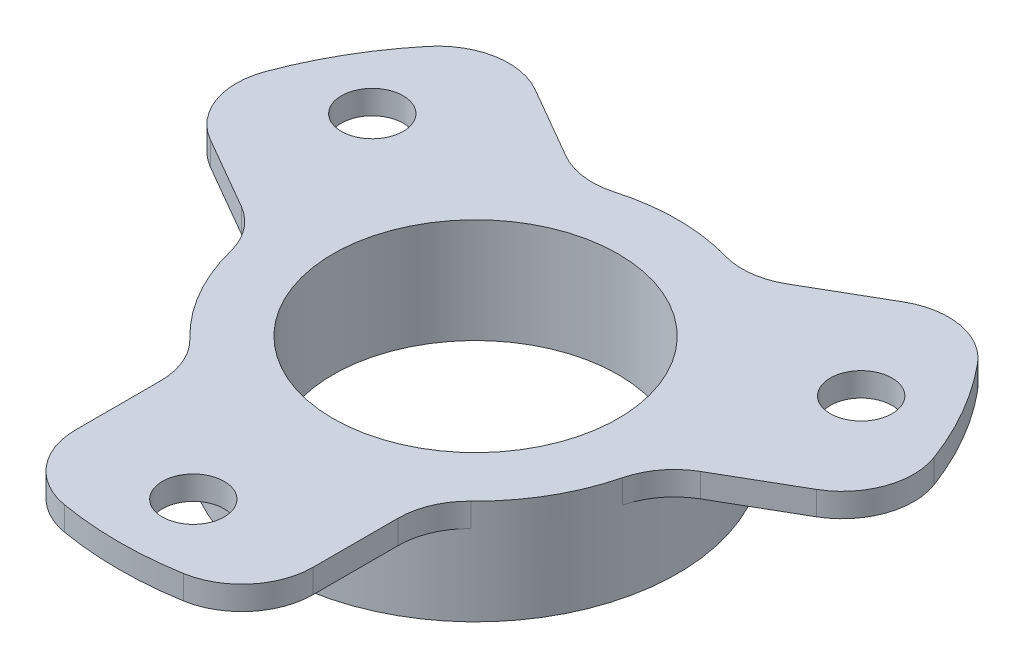
SolidWorks part; units mm, degrees
material "ABS"
ref_plane "Front Plane" through (0, 0, 0) normal (0, 0, 1) x (1, 0, 0)
ref_plane "Top Plane" through (0, 0, 0) normal (0, 1, 0) x (1, 0, 0)
ref_plane "Right Plane" through (0, 0, 0) normal (1, 0, 0) x (0, 0, -1)
sketch "Master Dimension Reference" plane through (0, 0, 0) normal (0, 1, 0) x (1, 0, 0)
  line L0 (0, 27.1168) -> (0, -27.1168) construction
  line L1 (-38.0934, 0) -> (38.0934, 0) construction
  line L2 (0, 0) -> (25.9808, 15) construction
  line L3 (0, 0) -> (-25.9808, 15) construction
  circle A0 centre (0, 0) radius 23.75 construction
  circle A1 centre (0, 0) radius 12 construction
  point P4 (0, 0)
  point P8 (0, 0)
  dimension "D1" = 47.5
  dimension "D2" = 24
sketch "Sketch2" plane through (0, 0, 0) normal (0, 0, 1) x (1, 0, 0)
  line L0 (-40, 0) -> (-17, 0)
  line L1 (-13.5, -6.8) -> (23.543, -6.8) construction
  line L2 (-15.5, -6.8) -> (-17, -6.8)
  line L3 (-38.0934, 0) -> (38.0934, 0) construction
  line L4 (0, 30.0771) -> (0, -30.0771) construction
  line L5 (-12, -18.8498) -> (-12, 22.8498) construction
  line L7 (-23.543, -6.8) -> (-15.5, -6.8) construction
  line L8 (12, 0) -> (-12, 0) construction
  line L9 (-23.75, -19.5868) -> (-23.75, 19.5868) construction
  line L10 (-40, -43.6771) -> (-40, 30.0771) construction
  line L11 (-12, 2) -> (-12, -6.8)
  line L12 (-12, -6.8) -> (-13.5, -6.8)
  line L13 (-17, -6.8) -> (-17, 0)
  line L14 (-17, -25.8462) -> (-17, 25.8462) construction
  line L15 (-40, 2) -> (-12, 2)
  line L16 (-40, 2) -> (-40, 0)
  line L17 (-15.5, 0) -> (-13.5, 0)
  line L19 (-13.5, -6.8) -> (-13.5, 0)
  line L20 (-15.5, -6.8) -> (-15.5, 0)
  point P11 (0, 0)
  point P16 (-12, 2)
  point P17 (0, -6.8)
  point P22 (-23.75, 0)
  point P25 (-40, -6.8)
  point P28 (-17, 0)
  dimension "D1" = 12
  dimension "D2" = 6.8
  dimension "D3" = 23.75
  dimension "D4" = 40
  dimension "D5" = 17
  dimension "D6" = 2
revolve "Revolve1" add sketch "Sketch2" angle 360 about L4
sketch "Top View Pattern Sketch" plane through (0, 0, 0) normal (0, 1, 0) x (1, 0, 0)
  line L0 (-10, -23.6643) -> (-10, -16.5227)
  line L1 (0, 27.1168) -> (0, -27.1168) construction
  line L2 (-19.3091, -0.3989) -> (-25.4939, 3.1719)
  line L3 (0, 0) -> (-25.9808, 15) construction
  line L4 (-9.3091, 16.9216) -> (-15.4939, 20.4924)
  line L5 (0, 17) -> (0, 39.2184) construction
  line L7 (9.3091, 16.9216) -> (15.4939, 20.4924)
  line L9 (19.3091, -0.3989) -> (25.4939, 3.1719)
  line L10 (10, -23.6643) -> (10, -16.5227)
  circle A18 centre (0, 0) radius 6
  arc A19 (-16.4893, -4.1355) -> (-11.8261, -12.2124) centre (0, 0) ccw
  arc A21 (-5, -29.5804) -> (5, -29.5804) centre (0, 0) ccw
  arc A22 (-23.1174, 19.1203) -> (-28.1174, 10.4601) centre (0, 0) ccw
  arc A23 (28.1174, 10.4601) -> (23.1174, 19.1203) centre (0, 0) ccw
  arc A24 (11.8261, -12.2124) -> (16.4893, -4.1355) centre (0, 0) ccw
  arc A25 (4.6632, 16.3479) -> (-4.6632, 16.3479) centre (0, 0) ccw
  arc A35 (-10, -23.6643) -> (-5, -29.5804) centre (-4, -23.6643) ccw
  arc A36 (-11.8261, -12.2124) -> (-10, -16.5227) centre (-16, -16.5227) cw
  arc A37 (-16.4893, -4.1355) -> (-19.3091, -0.3989) centre (-22.3091, -5.5951) ccw
  arc A38 (-25.4939, 3.1719) -> (-28.1174, 10.4601) centre (-22.4939, 8.3681) cw
  arc A39 (-23.1174, 19.1203) -> (-15.4939, 20.4924) centre (-18.4939, 15.2963) cw
  arc A40 (-9.3091, 16.9216) -> (-4.6632, 16.3479) centre (-6.3091, 22.1178) ccw
  arc A41 (4.6632, 16.3479) -> (9.3091, 16.9216) centre (6.3091, 22.1178) ccw
  arc A42 (15.4939, 20.4924) -> (23.1174, 19.1203) centre (18.4939, 15.2963) cw
  arc A43 (28.1174, 10.4601) -> (25.4939, 3.1719) centre (22.4939, 8.3681) cw
  arc A44 (19.3091, -0.3989) -> (16.4893, -4.1355) centre (22.3091, -5.5951) ccw
  arc A45 (11.8261, -12.2124) -> (10, -16.5227) centre (16, -16.5227) ccw
  arc A46 (10, -23.6643) -> (5, -29.5804) centre (4, -23.6643) cw
  point P1 (0, 0)
  point P22 (10, -13.7477)
  point P25 (10, -28.2843)
  point P28 (29.4949, 5.4819)
  point P31 (16.9059, -1.7864)
  point P34 (19.4949, 22.8024)
  point P37 (6.9059, 15.5341)
  point P40 (-19.4949, 22.8024)
  point P43 (-16.9059, -1.7864)
  point P47 (-6.9059, 15.5341)
  point P50 (-10, -13.7477)
  point P53 (-10, -28.2843)
  point P56 (-29.4949, 5.4819)
  dimension "D8" = 12
  dimension "D5" = 34
  dimension "D4" = 60
  dimension "D6" = 6
  dimension "D7" = 6
  dimension "D1" = 10
  dimension "D2" = 10
  dimension "D3" = 10
extrude "Cut-Extrude1" cut sketch "Top View Pattern Sketch" against normal mid plane 30 flip side to cut
hole_wizard "Ø4.0mm Dowel Hole1" positions "Sketch4" profile "Sketch5" hole size "Ø4.0" standard "ANSI Metric" end condition through all
sketch "Sketch4" plane through (0, 0, 0) normal (0, -1, 0) x (-1, 0, 0)
  line L0 (0, 27.1168) -> (0, -27.1168) construction
  line L1 (0, 0) -> (25.9808, 15) construction
  line L2 (0, 0) -> (-25.9808, 15) construction
  circle A0 centre (0, 0) radius 23.75 construction
  point P0 (0, -23.75)
  point P6 (20.5681, 11.875)
  point P10 (-20.5681, 11.875)
sketch "Sketch5" plane through (0, 0, 23.75) normal (1, 0, 0) x (0, 0, -1)
  line L0 (0, 0) -> (0, 2)
  line L1 (0, 2) -> (2.6, 2)
  line L2 (2.6, 2) -> (2.6, 0)
  line L5 (2.6, 0) -> (0, 0)
  line L11 (0, -6.35) -> (0, 107.95) construction
  dimension "Thru Hole Dia." = 5.2
  dimension "Thru Hole Depth" = 2
equation "\"D2@Top View Pattern Sketch\"=\"D1@Top View Pattern Sketch\""
equation "\"D3@Top View Pattern Sketch\"=\"D1@Top View Pattern Sketch\""
